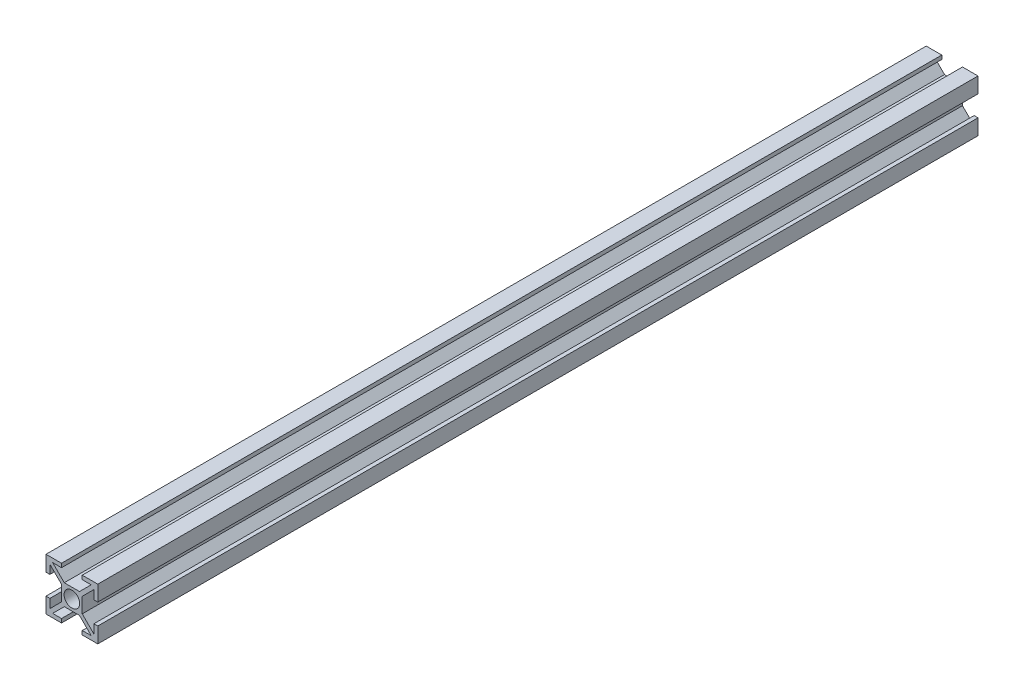
SolidWorks part; units mm, degrees
material "3.0205 (EN-AW 1200)"
ref_plane "Plano frontal" through (0, 0, 0) normal (0, 0, 1) x (1, 0, 0)
ref_plane "Plano superior" through (0, 0, 0) normal (0, 1, 0) x (1, 0, 0)
ref_plane "Plano direito" through (0, 0, 0) normal (1, 0, 0) x (0, 0, -1)
sketch "Esboço1" plane through (0, 0, 0) normal (0, 0, 1) x (1, 0, 0)
  line L0 (-2.9393, 4) -> (2.9393, 4)
  line L1 (-10, -10) -> (-4, -10)
  line L2 (-10, -10) -> (-10, -4)
  line L3 (-10, 10) -> (-4, 10)
  line L4 (10, -10) -> (10, -4)
  line L5 (-10, -10) -> (-4, -4) construction
  line L6 (-10, 10) -> (0, 0) construction
  line L7 (-7.4393, -8.5) -> (-2.9393, -4)
  line L8 (4, -10) -> (10, -10)
  line L9 (-8.5, -7.4393) -> (-4, -2.9393)
  line L10 (-8.5, 7.4393) -> (-4, 2.9393)
  line L11 (-7.4393, -8.5) -> (-4, -8.5)
  line L12 (-8.5, -7.4393) -> (-8.5, -4)
  line L13 (-7.4393, 8.5) -> (-4, 8.5)
  line L14 (8.5, -7.4393) -> (8.5, -4)
  line L17 (-4, 10) -> (-4, 8.5)
  line L18 (4, -8.5) -> (7.4393, -8.5)
  line L19 (-10, -4) -> (-8.5, -4)
  line L20 (4, 10) -> (4, 8.5)
  line L21 (-10, 4) -> (-8.5, 4)
  line L22 (-4, 2.9393) -> (-4, -2.9393)
  line L23 (-4, -8.5) -> (-4, -10)
  line L24 (-8.5, 4) -> (-8.5, 7.4393)
  line L25 (-10, 4) -> (-10, 10)
  line L26 (-7.4393, 8.5) -> (-2.9393, 4)
  line L27 (4, 8.5) -> (7.4393, 8.5)
  line L28 (-2.9393, -4) -> (2.9393, -4)
  line L29 (4, 10) -> (10, 10)
  line L30 (4, -8.5) -> (4, -10)
  line L31 (10, 4) -> (10, 10)
  line L32 (8.5, 4) -> (8.5, 7.4393)
  line L33 (-10.5303, -9.4697) -> (9.4697, 10.5303) construction
  line L34 (8.5, 4) -> (10, 4)
  line L35 (8.5, -4) -> (10, -4)
  line L36 (-10, -10) -> (10, 10) construction
  line L37 (4, 2.9393) -> (4, -2.9393)
  line L38 (-9.4697, -10.5303) -> (10.5303, 9.4697) construction
  line L40 (2.9393, -4) -> (7.4393, -8.5)
  line L41 (4, -4) -> (10, -10) construction
  line L43 (4, -2.9393) -> (8.5, -7.4393)
  line L44 (4, 0) -> (10, 0) construction
  line L45 (4, 2.9393) -> (8.5, 7.4393)
  line L47 (4, 4) -> (10, 10) construction
  line L48 (2.9393, 4) -> (7.4393, 8.5)
  circle A0 centre (0, 0) radius 3
  point P0 (0, 0)
  point P14 (-4.0323, -3.9672)
  dimension "D5" = 6
  dimension "D1" = 0.75
  dimension "D3" = 1.5
  dimension "D4" = 20
  dimension "D6" = 8
  dimension "D7" = 20
  dimension "D9" = 1.5
  dimension "D2" = 8
extrude "Ressalto-extrusão1" add sketch "Esboço1" along normal blind 340
